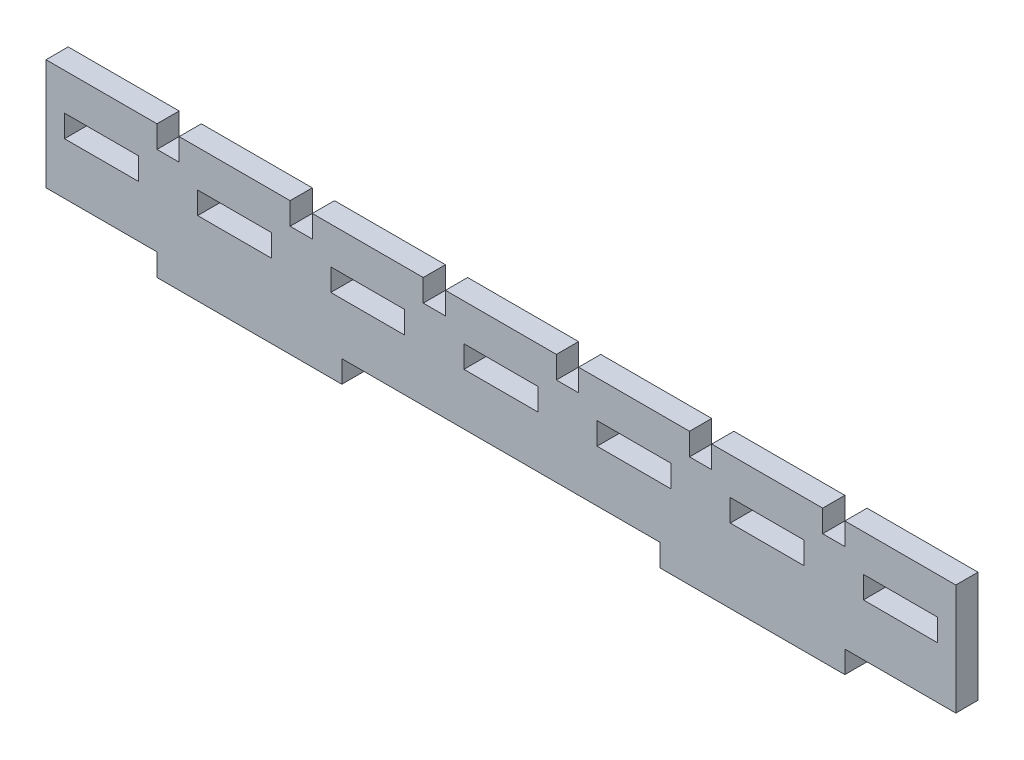
SolidWorks part; units mm, degrees
ref_plane "Front Plane" through (0, 0, 0) normal (0, 0, 1) x (1, 0, 0)
ref_plane "Top Plane" through (0, 0, 0) normal (0, 1, 0) x (1, 0, 0)
ref_plane "Right Plane" through (0, 0, 0) normal (1, 0, 0) x (0, 0, -1)
sketch "Sketch2" plane through (0, 0, 0) normal (0, 0, 1) x (1, 0, 0)
  line L0 (-43.5, 7.5) -> (-28.5, 7.5)
  line L1 (-61.5, 7.5) -> (-46.5, 7.5)
  line L2 (-61.5, 7.5) -> (-61.5, -7.5)
  line L3 (-61.5, -7.5) -> (-46.5, -7.5)
  line L4 (61.5, 7.5) -> (61.5, -7.5)
  line L5 (-25.5, 7.5) -> (-10.5, 7.5)
  line L6 (-21.5, -7.5) -> (-10, -7.5)
  line L7 (-59, 2.5) -> (-49, 2.5)
  line L8 (-59, 2.5) -> (-59, -0.5)
  line L9 (-59, -0.5) -> (-49, -0.5)
  line L10 (-49, 2.5) -> (-49, -0.5)
  line L11 (-7.5, 7.5) -> (7.5, 7.5)
  line L12 (10, -7.5) -> (21.5, -7.5)
  line L13 (-31, 2.5) -> (-31, -0.5)
  line L14 (-41, 2.5) -> (-41, -0.5)
  line L15 (10.5, 7.5) -> (25.5, 7.5)
  line L16 (-41, 2.5) -> (-31, 2.5)
  line L17 (-41, -0.5) -> (-31, -0.5)
  line L18 (28.5, 7.5) -> (43.5, 7.5)
  line L19 (-13, 2.5) -> (-13, -0.5)
  line L20 (-23, 2.5) -> (-23, -0.5)
  line L21 (-10, -7.5) -> (10, -7.5)
  line L22 (-23, 2.5) -> (-13, 2.5)
  line L23 (-23, -0.5) -> (-13, -0.5)
  line L24 (46.5, -7.5) -> (61.5, -7.5)
  line L25 (5, 2.5) -> (5, -0.5)
  line L26 (-5, 2.5) -> (-5, -0.5)
  line L27 (46.5, -7.5) -> (46.5, -10.5)
  line L28 (-5, 2.5) -> (5, 2.5)
  line L29 (-5, -0.5) -> (5, -0.5)
  line L30 (46.5, 7.5) -> (61.5, 7.5)
  line L31 (23, 2.5) -> (23, -0.5)
  line L32 (13, 2.5) -> (13, -0.5)
  line L34 (13, 2.5) -> (23, 2.5)
  line L35 (13, -0.5) -> (23, -0.5)
  line L37 (41, 2.5) -> (41, -0.5)
  line L38 (31, 2.5) -> (31, -0.5)
  line L40 (31, 2.5) -> (41, 2.5)
  line L41 (31, -0.5) -> (41, -0.5)
  line L43 (59, 2.5) -> (59, -0.5)
  line L44 (49, 2.5) -> (49, -0.5)
  line L46 (49, 2.5) -> (59, 2.5)
  line L47 (49, -0.5) -> (59, -0.5)
  line L50 (-46.5, -7.5) -> (-46.5, -10.5)
  line L51 (-46.5, -10.5) -> (-21.5, -10.5)
  line L52 (-21.5, -7.5) -> (-21.5, -10.5)
  line L55 (21.5, -10.5) -> (46.5, -10.5)
  line L57 (21.5, -7.5) -> (21.5, -10.5)
  line L58 (-25.5, 7.5) -> (-25.5, 4.5)
  line L70 (-46.5, 7.5) -> (-46.5, 4.5)
  line L71 (-46.5, 4.5) -> (-43.5, 4.5)
  line L72 (-43.5, 7.5) -> (-43.5, 4.5)
  line L75 (-28.5, 7.5) -> (-28.5, 4.5)
  line L76 (-28.5, 4.5) -> (-25.5, 4.5)
  line L77 (-7.5, 7.5) -> (-7.5, 4.5)
  line L78 (-10.5, 7.5) -> (-10.5, 4.5)
  line L79 (-10.5, 4.5) -> (-7.5, 4.5)
  line L80 (10.5, 7.5) -> (10.5, 4.5)
  line L81 (7.5, 7.5) -> (7.5, 4.5)
  line L82 (7.5, 4.5) -> (10.5, 4.5)
  line L83 (28.5, 7.5) -> (28.5, 4.5)
  line L84 (25.5, 7.5) -> (25.5, 4.5)
  line L85 (25.5, 4.5) -> (28.5, 4.5)
  line L86 (46.5, 7.5) -> (46.5, 4.5)
  line L87 (43.5, 7.5) -> (43.5, 4.5)
  line L88 (43.5, 4.5) -> (46.5, 4.5)
  point P0 (0, 0)
  point P6 (-54, 1)
  point P11 (-36, 1)
  point P16 (-18, 1)
  point P21 (0, 1)
  point P26 (18, 1)
  point P31 (36, 1)
  point P36 (54, 1)
  point P41 (-34, -7.5)
  point P47 (-45, 6)
  point P52 (0, -6)
  dimension "D1" = 123
  dimension "D2" = 15
extrude "Boss-Extrude2" add sketch "Sketch2" along normal blind 3
